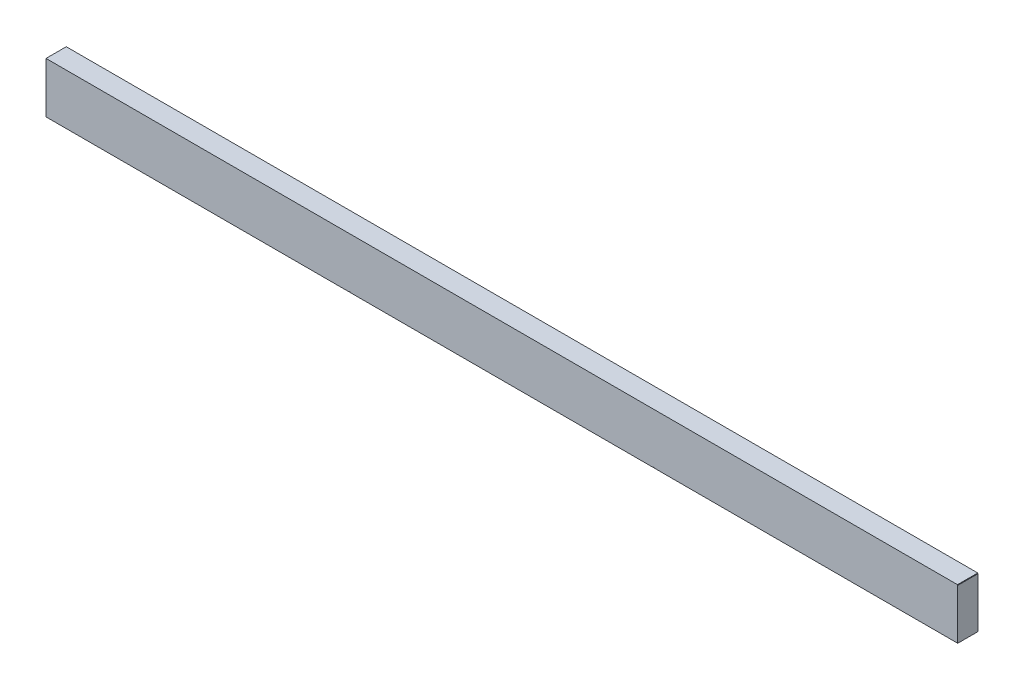
SolidWorks part; units mm, degrees
ref_plane "Front Plane" through (0, 0, 0) normal (0, 0, 1) x (1, 0, 0)
ref_plane "Top Plane" through (0, 0, 0) normal (0, 1, 0) x (1, 0, 0)
ref_plane "Right Plane" through (0, 0, 0) normal (1, 0, 0) x (0, 0, -1)
sketch "Sketch1" plane through (0, 0, 0) normal (1, 0, 0) x (0, 0, -1)
  line L1 (-100, -250) -> (100, -250)
  line L2 (-100, -250) -> (-100, 250)
  line L3 (-100, 250) -> (100, 250)
  line L4 (100, -250) -> (100, 250)
  line L5 (-100, -250) -> (100, 250) construction
  line L6 (-100, 250) -> (100, -250) construction
  point P0 (0, 0)
  dimension "D1" = 200
  dimension "D2" = 500
extrude "Boss-Extrude1" add sketch "Sketch1" along normal blind 9000
sketch "Sketch2" plane through (0, 0, 100) normal (0, 0, 1) x (1, 0, 0)
  line L0 (9000, -250) -> (0, -250) construction
  line L1 (2997.5, -255) -> (3002.5, -255)
  line L2 (2997.5, -255) -> (2997.5, -245)
  line L3 (2997.5, -245) -> (3002.5, -245)
  line L4 (3002.5, -255) -> (3002.5, -245)
  line L5 (2997.5, -255) -> (3002.5, -245) construction
  line L6 (2997.5, -245) -> (3002.5, -255) construction
  line L7 (0, 250) -> (0, -250) construction
  line L8 (5997.5, -255) -> (6002.5, -255)
  line L9 (5997.5, -255) -> (5997.5, -245)
  line L10 (5997.5, -245) -> (6002.5, -245)
  line L11 (6002.5, -255) -> (6002.5, -245)
  line L12 (5997.5, -255) -> (6002.5, -245) construction
  line L13 (5997.5, -245) -> (6002.5, -255) construction
  line L14 (9000, 250) -> (0, 250) construction
  line L15 (8997.5, 245) -> (9002.5, 245)
  line L16 (8997.5, 245) -> (8997.5, 255)
  line L17 (8997.5, 255) -> (9002.5, 255)
  line L18 (9002.5, 245) -> (9002.5, 255)
  line L19 (8997.5, 245) -> (9002.5, 255) construction
  line L20 (8997.5, 255) -> (9002.5, 245) construction
  point P0 (3000, -250)
  point P7 (6000, -250)
  point P14 (9000, -250)
  point P20 (9000, -250)
  point P21 (9000, -250)
  point P22 (0, 0)
  dimension "D1" = 3000
  dimension "D2" = 3000
  dimension "D3" = 5
  dimension "D4" = 10
  dimension "D5" = 5
  dimension "D6" = 10
  dimension "D7" = 10
  dimension "D8" = 5
  dimension "D9" = 5
extrude "Cut-Extrude1" cut sketch "Sketch2" against normal through all
